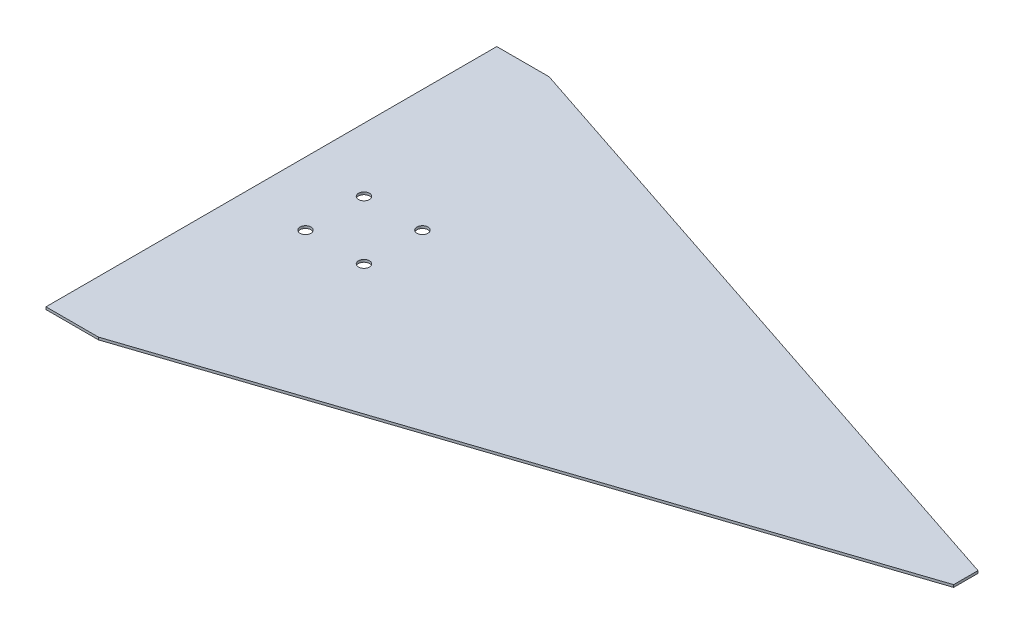
SolidWorks part; units mm, degrees
ref_plane "Front Plane" through (0, 0, 0) normal (0, 0, 1) x (1, 0, 0)
ref_plane "Top Plane" through (0, 0, 0) normal (0, 1, 0) x (1, 0, 0)
ref_plane "Right Plane" through (0, 0, 0) normal (1, 0, 0) x (0, 0, -1)
sketch "Sketch2" plane through (0, 0, 0) normal (0, 1, 0) x (1, 0, 0)
  line L0 (-121, 92.5) -> (142.5, 5)
  line L1 (-142.5, 92.5) -> (-121, 92.5)
  line L2 (-142.5, 92.5) -> (-142.5, -92.5)
  line L3 (-142.5, -92.5) -> (-121, -92.5)
  line L4 (142.5, 5) -> (142.5, -5)
  line L5 (-142.5, 92.5) -> (-121, 92.5)
  line L6 (-142.5, 92.5) -> (-142.5, -92.5)
  line L7 (-142.5, -92.5) -> (-121, -92.5)
  line L9 (-121, -92.5) -> (142.5, -5)
extrude "Boss-Extrude1" add sketch "Sketch2" along normal blind 1 contours L3 L9 L4 L0 L1 L2
sketch "Sketch3" plane through (0, 1, 0) normal (0, 1, 0) x (1, 0, 0)
  circle A0 centre (-116.5, 12) radius 2.25
  circle A1 centre (-92.5, 12) radius 2.25
  circle A2 centre (-116.5, -12) radius 2.25
  circle A3 centre (-92.5, -12) radius 2.25
extrude "Cut-Extrude1" cut sketch "Sketch3" against normal blind 1
